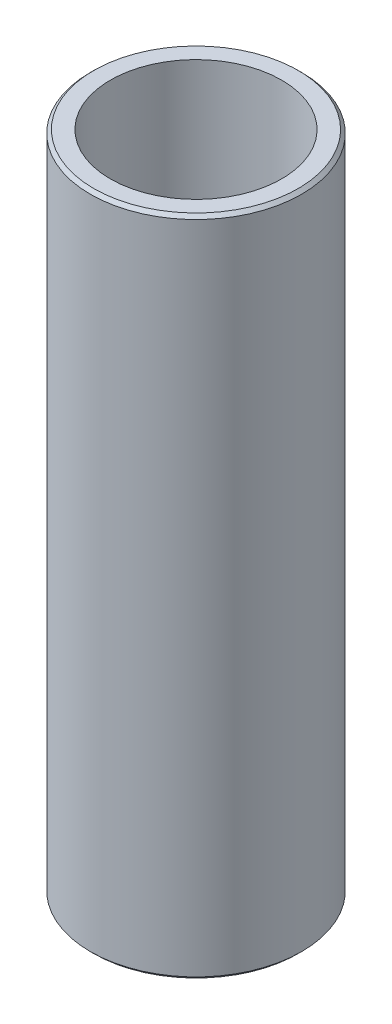
SolidWorks part; units mm, degrees
ref_plane "Front Plane" through (0, 0, 0) normal (0, 0, 1) x (1, 0, 0)
ref_plane "Top Plane" through (0, 0, 0) normal (0, 1, 0) x (1, 0, 0)
ref_plane "Right Plane" through (0, 0, 0) normal (1, 0, 0) x (0, 0, -1)
sketch "Sketch1" plane through (0, 0, 0) normal (0, 1, 0) x (1, 0, 0)
  circle A0 centre (0, 0) radius 7.94
  circle A1 centre (0, 0) radius 6.44
  dimension "D1" = 15.88
  dimension "D2" = 1.5
extrude "Boss-Extrude1" add sketch "Sketch1" along normal blind 49.82
chamfer "Chamfer1" distance 0.25 angle 45 2 edges at (0, 0, 7.94) (0, 49.82, 7.94)
